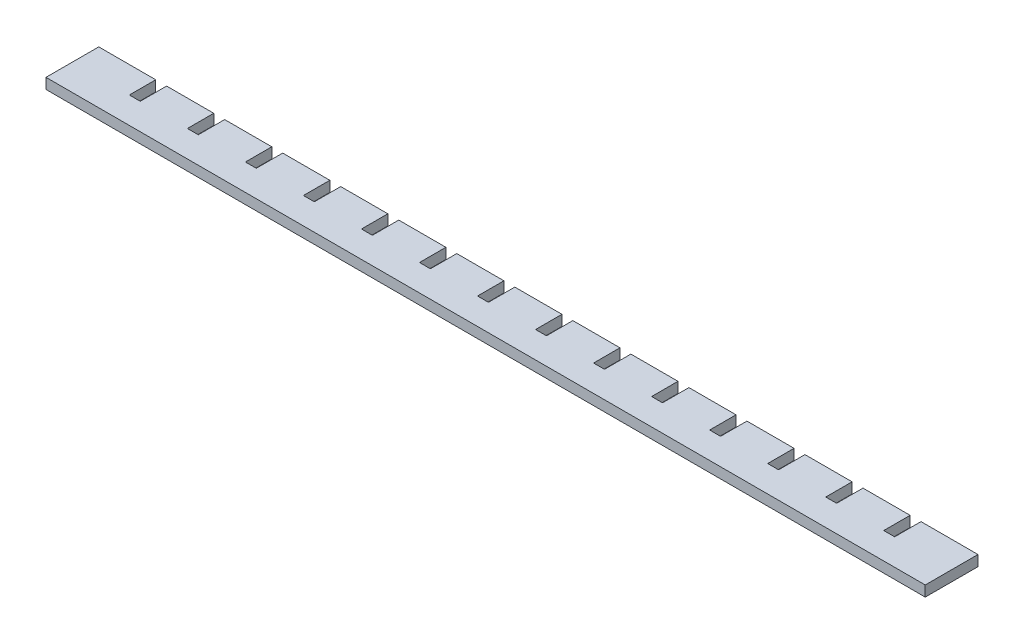
SolidWorks part; units mm, degrees
ref_plane "Ebene vorne" through (0, 0, 0) normal (0, 0, 1) x (1, 0, 0)
ref_plane "Ebene oben" through (0, 0, 0) normal (0, 1, 0) x (1, 0, 0)
ref_plane "Ebene rechts" through (0, 0, 0) normal (1, 0, 0) x (0, 0, -1)
sketch "Skizze1" plane through (0, 0, 0) normal (0, 1, 0) x (1, 0, 0)
  line L0 (4.8859, 7.8015) -> (4.8859, 0.3015)
  line L1 (-27.8141, 7.8015) -> (-11.6141, 7.8015)
  line L2 (-27.8141, 7.8015) -> (-27.8141, -7.1985)
  line L3 (-27.8141, -7.1985) -> (222.1859, -7.1985)
  line L4 (222.1859, 7.8015) -> (222.1859, -7.1985)
  line L6 (-11.6141, 7.8015) -> (-11.6141, 0.3015)
  line L7 (-11.6141, 0.3015) -> (-8.5141, 0.3015)
  line L8 (-8.5141, 7.8015) -> (-8.5141, 0.3015)
  line L9 (4.8859, 0.3015) -> (7.9859, 0.3015)
  line L10 (7.9859, 7.8015) -> (7.9859, 0.3015)
  line L11 (21.3859, 7.8015) -> (21.3859, 0.3015)
  line L12 (21.3859, 0.3015) -> (24.4859, 0.3015)
  line L13 (24.4859, 7.8015) -> (24.4859, 0.3015)
  line L14 (37.8859, 7.8015) -> (37.8859, 0.3015)
  line L15 (37.8859, 0.3015) -> (40.9859, 0.3015)
  line L16 (40.9859, 7.8015) -> (40.9859, 0.3015)
  line L17 (54.3859, 7.8015) -> (54.3859, 0.3015)
  line L18 (54.3859, 0.3015) -> (57.4859, 0.3015)
  line L19 (57.4859, 7.8015) -> (57.4859, 0.3015)
  line L20 (70.8859, 7.8015) -> (70.8859, 0.3015)
  line L21 (70.8859, 0.3015) -> (73.9859, 0.3015)
  line L22 (73.9859, 7.8015) -> (73.9859, 0.3015)
  line L23 (87.3859, 7.8015) -> (87.3859, 0.3015)
  line L24 (87.3859, 0.3015) -> (90.4859, 0.3015)
  line L25 (90.4859, 7.8015) -> (90.4859, 0.3015)
  line L26 (103.8859, 7.8015) -> (103.8859, 0.3015)
  line L27 (103.8859, 0.3015) -> (106.9859, 0.3015)
  line L28 (106.9859, 7.8015) -> (106.9859, 0.3015)
  line L29 (120.3859, 7.8015) -> (120.3859, 0.3015)
  line L30 (120.3859, 0.3015) -> (123.4859, 0.3015)
  line L31 (123.4859, 7.8015) -> (123.4859, 0.3015)
  line L32 (136.8859, 7.8015) -> (136.8859, 0.3015)
  line L33 (136.8859, 0.3015) -> (139.9859, 0.3015)
  line L34 (139.9859, 7.8015) -> (139.9859, 0.3015)
  line L35 (153.3859, 7.8015) -> (153.3859, 0.3015)
  line L36 (153.3859, 0.3015) -> (156.4859, 0.3015)
  line L37 (156.4859, 7.8015) -> (156.4859, 0.3015)
  line L38 (169.8859, 7.8015) -> (169.8859, 0.3015)
  line L39 (169.8859, 0.3015) -> (172.9859, 0.3015)
  line L40 (172.9859, 7.8015) -> (172.9859, 0.3015)
  line L41 (186.3859, 7.8015) -> (186.3859, 0.3015)
  line L42 (186.3859, 0.3015) -> (189.4859, 0.3015)
  line L43 (189.4859, 7.8015) -> (189.4859, 0.3015)
  line L44 (202.8859, 7.8015) -> (202.8859, 0.3015)
  line L45 (202.8859, 0.3015) -> (205.9859, 0.3015)
  line L46 (205.9859, 7.8015) -> (205.9859, 0.3015)
  line L47 (-8.5141, 7.8015) -> (4.8859, 7.8015)
  line L48 (7.9859, 7.8015) -> (21.3859, 7.8015)
  line L49 (24.4859, 7.8015) -> (37.8859, 7.8015)
  line L50 (219.3859, 7.8015) -> (219.3859, 0.3015) [skipped]
  line L51 (222.4859, 7.8015) -> (222.4859, 0.3015) [skipped]
  line L52 (219.3859, 0.3015) -> (222.4859, 0.3015) [skipped]
  line L53 (40.9859, 7.8015) -> (54.3859, 7.8015)
  line L54 (57.4859, 7.8015) -> (70.8859, 7.8015)
  line L55 (73.9859, 7.8015) -> (87.3859, 7.8015)
  line L56 (90.4859, 7.8015) -> (103.8859, 7.8015)
  line L57 (106.9859, 7.8015) -> (120.3859, 7.8015)
  line L58 (123.4859, 7.8015) -> (136.8859, 7.8015)
  line L59 (139.9859, 7.8015) -> (153.3859, 7.8015)
  line L60 (156.4859, 7.8015) -> (169.8859, 7.8015)
  line L61 (172.9859, 7.8015) -> (186.3859, 7.8015)
  line L62 (189.4859, 7.8015) -> (202.8859, 7.8015)
  line L63 (205.9859, 7.8015) -> (222.1859, 7.8015)
  dimension "D1" = 15
  dimension "D2" = 250
  dimension "D3" = 16.2
  dimension "D4" = 3.1
  dimension "D5" = 7.5
  dimension "D6" = 15
extrude "Aufsatz-Linear austragen1" add sketch "Skizze1" along normal blind 3
